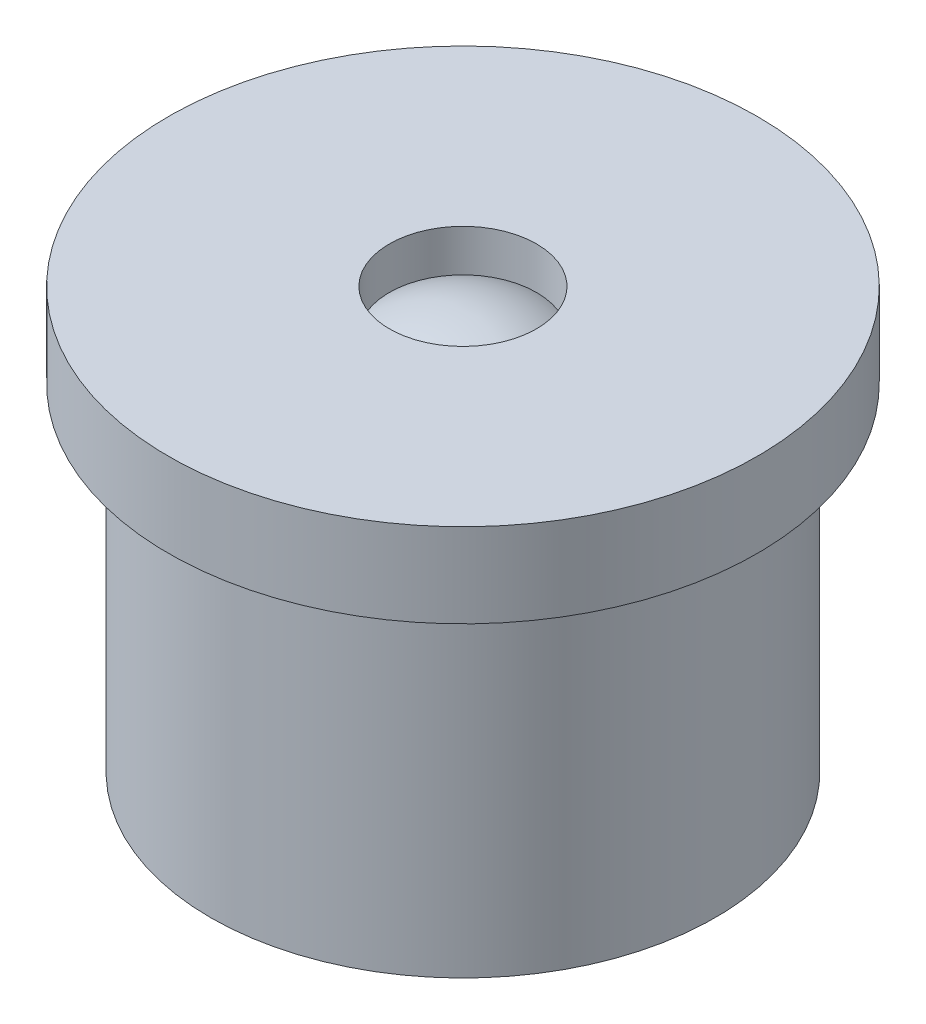
SolidWorks part; units mm, degrees
ref_plane "Front Plane" through (0, 0, 0) normal (0, 0, 1) x (1, 0, 0)
ref_plane "Top Plane" through (0, 0, 0) normal (0, 1, 0) x (1, 0, 0)
ref_plane "Right Plane" through (0, 0, 0) normal (1, 0, 0) x (0, 0, -1)
sketch "Sketch1" plane through (0, 0, 0) normal (1, 0, 0) x (0, 0, -1)
  line L0 (0, 0) -> (0, 17.7459) construction
  line L2 (1.75, 9) -> (1.75, 10)
  line L3 (1.75, 10) -> (7, 10)
  line L4 (7, 10) -> (7, 8)
  line L5 (7, 8) -> (6, 8)
  line L6 (6, 8) -> (6, 0)
  line L7 (6, 0) -> (0, 0)
  line L8 (0, 0) -> (0, 9.5)
  arc A0 (0, 9.5) -> (1.75, 9) centre (0, 6.1875) cw
  dimension "D1" = 14
  dimension "D2" = 10
  dimension "D3" = 3.5
  dimension "D4" = 0.5
  dimension "D5" = 0.5
  dimension "D6" = 2
  dimension "D7" = 12
revolve "Revolve1" add sketch "Sketch1" angle 360 about L0
sketch "Sketch2" plane through (0, 0, 0) normal (0, 0, 1) x (1, 0, 0)
  line L0 (0, 10) -> (19.257, 110)
  line L1 (1.75, 10) -> (-1.75, 10) construction
  line L2 (19.257, 110) -> (-19.257, 110)
  line L3 (-19.257, 110) -> (0, 10)
  line L4 (0, 10) -> (0, 110) construction
  line L5 (7, 10) -> (-7, 10) construction
  dimension "D1" = 21.8
  dimension "D2" = 100
sketch "Sketch3" plane through (0, 0, 0) normal (1, 0, 0) x (0, 0, -1)
  line L0 (0, 10) -> (25.6756, 110)
  line L1 (1.75, 10) -> (-1.75, 10) construction
  line L2 (25.6756, 110) -> (-25.6756, 110)
  line L3 (-25.6756, 110) -> (0, 10)
  line L4 (0, 10) -> (0, 110) construction
  line L5 (7, 10) -> (-7, 10) construction
  dimension "D1" = 28.8
  dimension "D2" = 100
